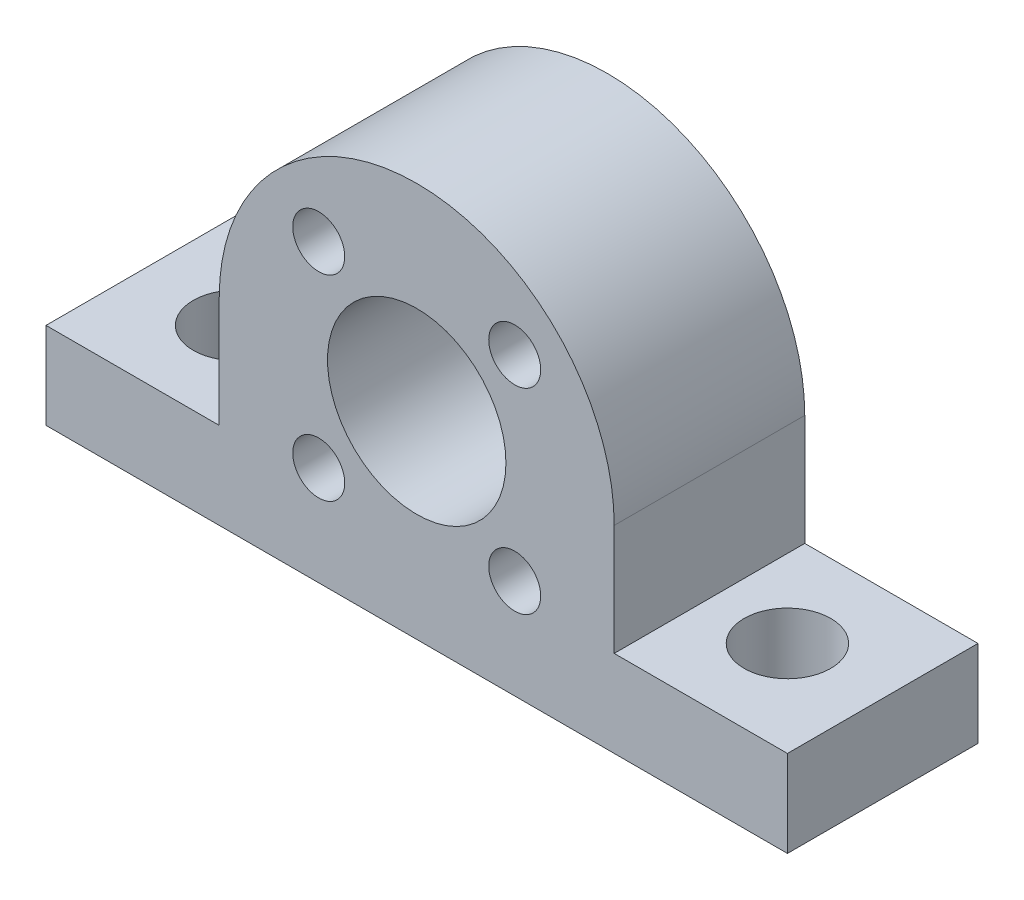
SolidWorks part; units mm, degrees
ref_plane "Front Plane" through (0, 0, 0) normal (0, 0, 1) x (1, 0, 0)
ref_plane "Top Plane" through (0, 0, 0) normal (0, 1, 0) x (1, 0, 0)
ref_plane "Right Plane" through (0, 0, 0) normal (1, 0, 0) x (0, 0, -1)
sketch "Sketch1" plane through (0, 0, 0) normal (0, 0, 1) x (1, 0, 0)
  line L0 (-21.4, -6.4) -> (-11.4, -6.4)
  line L3 (-21.4, -6.4) -> (-21.4, -11.4)
  line L4 (-21.4, -11.4) -> (21.4, -11.4)
  line L5 (0, 11.4) -> (0, -11.4) construction
  line L6 (21.4, -6.4) -> (21.4, -11.4)
  line L7 (21.4, -6.4) -> (11.4, -6.4)
  line L9 (-11.4, 0) -> (-11.4, -6.4)
  line L10 (11.4, 0) -> (11.4, -6.4)
  line L11 (0, 0) -> (-7.7782, 7.7782) construction
  line L12 (0, 0) -> (-11, 0) construction
  circle A0 centre (0, 0) radius 11 construction
  circle A1 centre (0, 0) radius 5.15
  arc A4 (-11.4, 0) -> (11.4, 0) centre (0, 0) cw
  circle A5 centre (-5.6569, 5.6569) radius 1.5
  circle A6 centre (5.6569, 5.6569) radius 1.5
  circle A7 centre (-5.6569, -5.6569) radius 1.5
  circle A8 centre (5.6569, -5.6569) radius 1.5
  point P6 (0, 11.4)
  dimension "D1" = 22
  dimension "D5" = 10.3
  dimension "D7" = 8
  dimension "D8" = 3
  dimension "D2" = 10
  dimension "D3" = 45
  dimension "D4" = 11.4
  dimension "D6" = 5
  dimension "D9" = 42.8
extrude "Boss-Extrude1" add sketch "Sketch1" along normal blind 11
sketch "Sketch2" plane through (0, -6.4, 0) normal (0, 1, 0) x (1, 0, 0)
  line L0 (0, 0) -> (0, -11) construction
  line L1 (-11.4, -11) -> (11.4, -11) construction
  line L2 (-11.4, 0) -> (-21.4, 0) construction
  line L3 (-21.4, -11) -> (-21.4, 0) construction
  circle A0 centre (-15.9, -5.5) radius 2.5
  circle A1 centre (15.9, -5.5) radius 2.5
  point P7 (0, 0)
  point P10 (-16.4, 0)
  point P11 (0, 0)
  point P14 (-21.4, -5.5)
  point P15 (0, 0)
  dimension "D1" = 5
  dimension "D2" = 5.5
extrude "Cut-Extrude1" cut sketch "Sketch2" against normal through all
